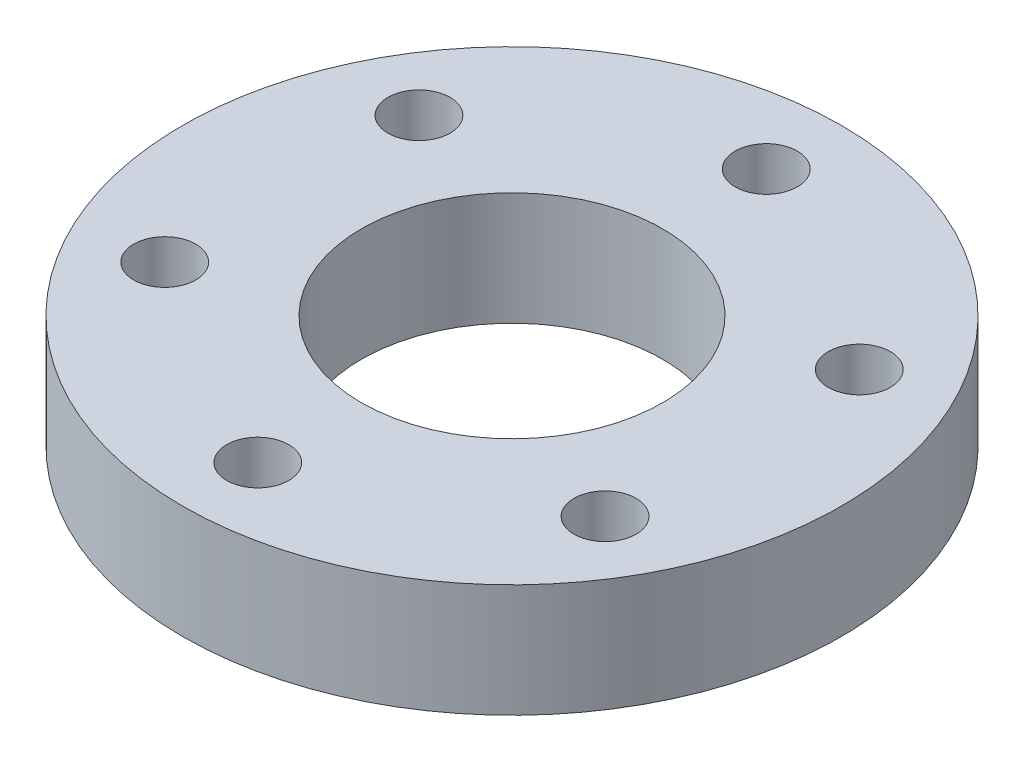
SolidWorks part; units mm, degrees
ref_plane "前视基准面" through (0, 0, 0) normal (0, 0, 1) x (1, 0, 0)
ref_plane "上视基准面" through (0, 0, 0) normal (0, 1, 0) x (1, 0, 0)
ref_plane "右视基准面" through (0, 0, 0) normal (1, 0, 0) x (0, 0, -1)
other "Configuration Table"
sketch "草图1" plane through (0, 0, 0) normal (0, 1, 0) x (1, 0, 0)
  circle A0 centre (0, 0) radius 17.5
  circle A1 centre (0, 0) radius 8
  circle A2 centre (0, 0) radius 13.5 construction
  circle A3 centre (0, 13.5) radius 1.65
  circle A4 centre (11.6913, 6.75) radius 1.65
  circle A5 centre (11.6913, -6.75) radius 1.65
  circle A6 centre (0, -13.5) radius 1.65
  circle A7 centre (-11.6913, -6.75) radius 1.65
  circle A8 centre (-11.6913, 6.75) radius 1.65
  point P7 (-18.1886, 7.9708)
  point P8 (0, 0)
  point P20 (0, 0)
  dimension "D1" = 35
  dimension "D2" = 16
  dimension "D3" = 27
  dimension "D4" = 3.3
  dimension "D5" = 6
extrude "凸台-拉伸1" add sketch "草图1" along normal blind 6
